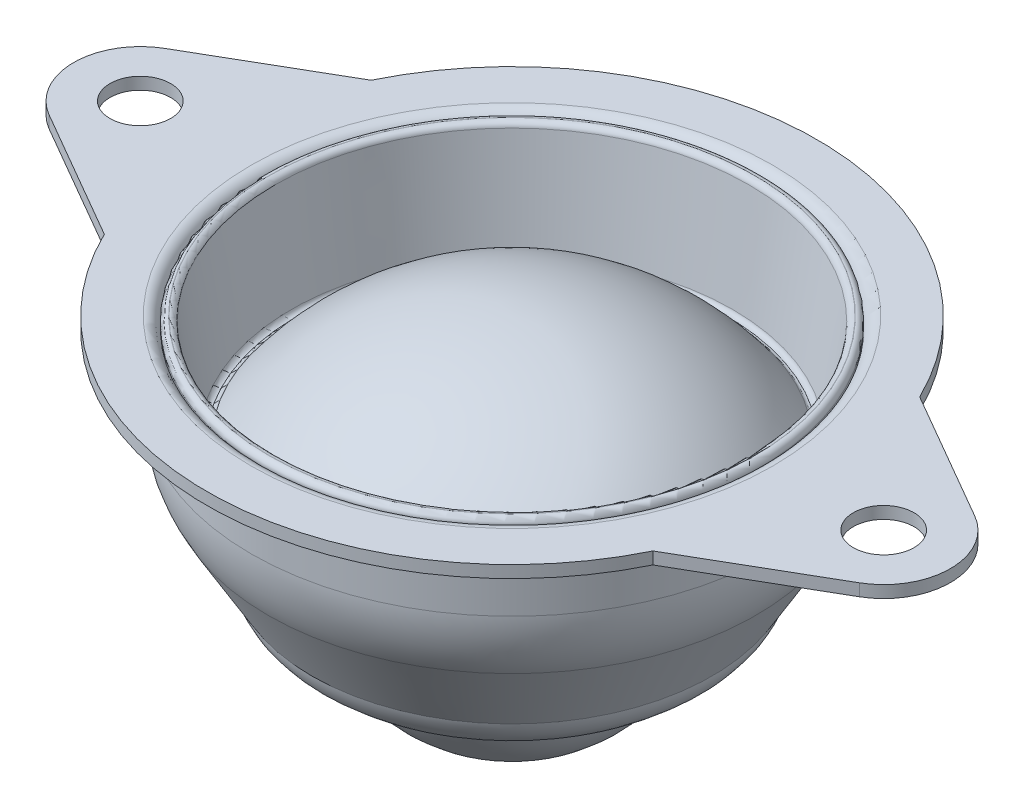
SolidWorks part; units mm, degrees
ref_plane "Alzado" through (0, 0, 0) normal (0, 0, 1) x (1, 0, 0)
ref_plane "Planta" through (0, 0, 0) normal (0, 1, 0) x (1, 0, 0)
ref_plane "Vista lateral" through (0, 0, 0) normal (1, 0, 0) x (0, 0, -1)
sketch "Croquis1" plane through (0, 0, 0) normal (1, 0, 0) x (0, 0, -1)
  line L0 (0, 0) -> (0, -20.5) construction
  line L1 (0, 0) -> (-25.15, 0) construction
  line L2 (-25.15, -1) -> (-22.5, -1)
  line L3 (-21.5, 0) -> (-25.15, 0)
  line L4 (-25.15, 0) -> (-25.15, -1)
  line L5 (-21.5, -2) -> (-21.5, -6.2769)
  line L6 (-16.5, -17.5) -> (-20.1193, -11.3471)
  line L7 (-20.5, -1) -> (-20.5, -5.6887)
  line L8 (-19.1193, -10.7589) -> (-15.5, -16.9118)
  line L9 (-12, -20.5) -> (-12, -19.5)
  line L10 (-20.5, -8.4118) -> (-21.5, -9) construction
  line L11 (-15.5, -16.9118) -> (-16.5, -17.5) construction
  arc A0 (-16.5, -17.5) -> (-12, -20.5) centre (-12.615, -16.5476) ccw
  arc A1 (-15.5, -16.9118) -> (-12, -19.5) centre (-10.7089, -14.0935) ccw
  arc A2 (-20.5, -5.6887) -> (-19.1193, -10.7589) centre (-10.5, -5.6887) ccw
  arc A3 (-20.1193, -11.3471) -> (-21.5, -6.2769) centre (-11.5, -6.2769) cw
  arc A4 (-20.5, -1) -> (-21.5, 0) centre (-21.5, -1) ccw
  arc A5 (-22.5, -1) -> (-21.5, -2) centre (-22.5, -2) cw
  point P23 (-20.5, 0)
  point P26 (-21.5, -1)
  dimension "D6" = 1
  dimension "D9" = 4
  dimension "D12" = 10
  dimension "D13" = 1
  dimension "D1" = 20.5
  dimension "D2" = 50.3
  dimension "D3" = 43
  dimension "D4" = 17.5
  dimension "D5" = 1
  dimension "D7" = 9
  dimension "D8" = 1
  dimension "D10" = 24
  dimension "D11" = 33
revolve "Revolución1" add sketch "Croquis1" angle 360 about L0
sketch "Croquis2" plane through (0, 0, 0) normal (0, 1, 0) x (1, 0, 0)
  line L0 (33.4037, 4.761) -> (22.6169, 11)
  line L1 (22.6169, -11) -> (33.4037, -4.761)
  line L2 (0, 20.5) -> (0, -20.5) construction
  line L3 (-22.6169, -11) -> (-33.4037, -4.761)
  line L4 (-33.4037, 4.761) -> (-22.6169, 11)
  arc A0 (33.4037, -4.761) -> (33.4037, 4.761) centre (30.65, 0) ccw
  circle A1 centre (0, 0) radius 25.15 construction
  arc A2 (22.6169, 11) -> (22.6169, -11) centre (0, 0) cw
  circle A3 centre (30.65, 0) radius 2.5
  circle A4 centre (0, 0) radius 20.5 construction
  circle A5 centre (0, 0) radius 20.5 construction
  circle A6 centre (-30.65, 0) radius 2.5
  arc A7 (-22.6169, 11) -> (-22.6169, -11) centre (0, 0) ccw
  arc A8 (-33.4037, -4.761) -> (-33.4037, 4.761) centre (-30.65, 0) cw
  dimension "D1" = 11
  dimension "D3" = 5
  dimension "D2" = 22
extrude "Saliente-Extruir1" add sketch "Croquis2" against normal blind 1
sketch "Croquis3" plane through (0, 0, 0) normal (1, 0, 0) x (0, 0, -1)
  line L0 (0, 0) -> (0, -20.5) construction
  line L1 (-12, -20.5) -> (12, -20.5) construction
  line L2 (-20.5092, -0.5674) -> (-19, -10)
  line L3 (21.5, 0) -> (-21.5, 0) construction
  line L4 (-19, -10) -> (-17.6, -10)
  line L5 (-20.5, -1) -> (20.5, -1) construction
  line L6 (-11, 0) -> (-25.15, 0) construction
  line L7 (-20.0254, 0) -> (-20.0051, 0)
  line L8 (-19.5213, -0.4126) -> (-18.2012, -8.6632)
  line L9 (-17.8062, -9) -> (-17.8034, -9)
  line L10 (0, 0) -> (0, -1)
  arc A0 (-17.6, -10) -> (0, -1) centre (0, -22.7089) cw
  arc A1 (-17.4813, -8.8372) -> (0, 0) centre (0, -21.7089) cw
  arc A2 (-18.2012, -8.6632) -> (-17.8062, -9) centre (-17.8062, -8.6) ccw
  arc A3 (-17.8034, -9) -> (-17.4813, -8.8372) centre (-17.8034, -8.6) ccw
  arc A4 (-20.5092, -0.5674) -> (-20.0254, 0) centre (-20.0254, -0.49) cw
  arc A5 (-20.0051, 0) -> (-19.5213, -0.4126) centre (-20.0051, -0.49) cw
  point P24 (-17.6, -9)
  point P27 (-20.6, 0)
  point P30 (-19.5873, 0)
  dimension "D3" = 1
  dimension "D8" = 0.4
  dimension "D9" = 0.49
  dimension "D1" = 38
  dimension "D2" = 35.2
  dimension "D4" = 10
  dimension "D5" = 1.6
  dimension "D6" = 1
  dimension "D7" = 1
revolve "Revolución2" add sketch "Croquis3" angle 360 about L0
sketch "Croquis4" plane through (0, 0, 0) normal (1, 0, 0) x (0, 0, -1)
  line L0 (0, 0) -> (0, -16.85) construction
  line L4 (0, -16.85) -> (0, -29.1) construction
  line L6 (-12, -20.5) -> (12, -20.5) construction
  line L7 (0, -4.6) -> (0, -29.1)
  arc A0 (0, -4.6) -> (0, -29.1) centre (0, -16.85) cw
  dimension "D1" = 12.25
  dimension "D2" = 8.6
revolve "Revolución3" add sketch "Croquis4" angle 360 about L7
